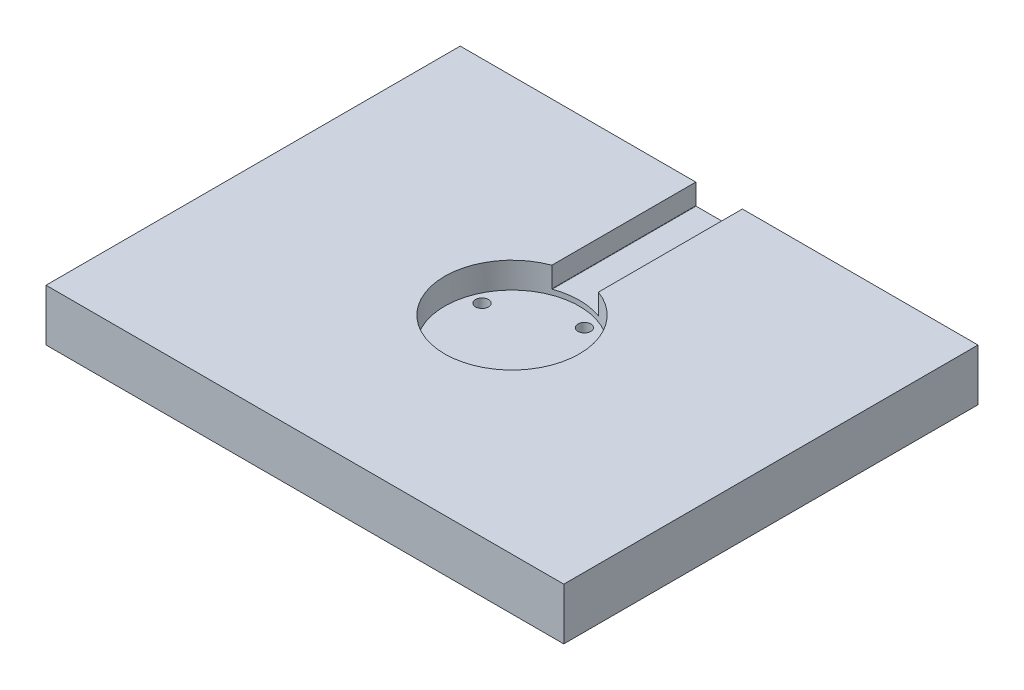
SolidWorks part; units mm, degrees
material "6061-T4 (SS)"
ref_plane "Front Plane" through (0, 0, 0) normal (0, 0, 1) x (1, 0, 0)
ref_plane "Top Plane" through (0, 0, 0) normal (0, 1, 0) x (1, 0, 0)
ref_plane "Right Plane" through (0, 0, 0) normal (1, 0, 0) x (0, 0, -1)
sketch "Sketch1" plane through (0, 0, 0) normal (0, 1, 0) x (1, 0, 0)
  line L1 (100, 80) -> (-100, 80)
  line L2 (100, 80) -> (100, -80)
  line L3 (100, -80) -> (-100, -80)
  line L4 (-100, 80) -> (-100, -80)
  line L5 (100, 80) -> (-100, -80) construction
  line L6 (100, -80) -> (-100, 80) construction
  point P0 (0, 0)
  dimension "D1" = 160
  dimension "D2" = 200
extrude "base" add sketch "Sketch1" along normal blind 20
sketch "Sketch2" plane through (0, 20, 0) normal (0, 1, 0) x (1, 0, 0)
  circle A0 centre (0, 0) radius 26
  dimension "D1" = 52
extrude "load cell cut" cut sketch "Sketch2" against normal blind 10 contours A0
sketch "post positioning points" plane through (0, 20, 0) normal (0, 1, 0) x (1, 0, 0)
  line L0 (-100, 80) -> (-100, -80) construction
  line L1 (-100, -80) -> (100, -80) construction
  line L2 (100, -80) -> (100, 80) construction
  line L3 (100, 80) -> (-100, 80) construction
  point P0 (-85, -65)
  point P5 (-25, 65)
  point P6 (-85, 65)
  point P7 (85, 65)
  point P8 (85, -65)
  point P9 (0, -65)
  point P10 (25, 65)
  dimension "D1" = 15
  dimension "D2" = 15
  dimension "D3" = 15
  dimension "D4" = 15
  dimension "D5" = 85
  dimension "D7" = 60
  dimension "D6" = 60
sketch "Sketch6" plane through (0, 0, -80) normal (0, 0, 1) x (1, 0, 0)
  line L0 (-100, 0) -> (100, 0) construction
  line L1 (9, 20) -> (-9, 20)
  line L2 (9, 20) -> (9, 12)
  line L3 (9, 12) -> (-9, 12)
  line L4 (-9, 20) -> (-9, 12)
  line L5 (9, 20) -> (-9, 12) construction
  line L6 (9, 12) -> (-9, 20) construction
  line L7 (-100, 20) -> (100, 20) construction
  point P0 (0, 16)
  point P8 (0, 0)
  dimension "D1" = 18
  dimension "D2" = 8
extrude "cut wire" cut sketch "Sketch6" along normal up to next contours L4 L3 L2 L1
sketch "Sketch7" plane through (0, 0, -80) normal (0, 0, 1) x (1, 0, 0)
  line L1 (5, 20) -> (-5, 20)
  line L2 (5, 20) -> (5, 10)
  line L3 (5, 10) -> (-5, 10)
  line L4 (-5, 20) -> (-5, 10)
  line L5 (5, 20) -> (-5, 10) construction
  line L6 (5, 10) -> (-5, 20) construction
  line L7 (-100, 0) -> (100, 0) construction
  line L8 (-100, 20) -> (100, 20) construction
  point P0 (0, 15)
  point P8 (0, 0)
  dimension "D1" = 10
  dimension "D2" = 10
extrude "cut wire 2" [suppressed] cut sketch "Sketch7" along normal up to next
fillet "Fillet5" [suppressed] radius 10
fillet "Fillet6" radius 0.1 2 edges at (9, 12, -52.1963) (-9, 12, -52.1963)
fillet "Fillet7" [suppressed] radius 5
sketch "Sketch12" plane through (0, 0, 0) normal (0, -1, 0) x (1, 0, 0)
  line L0 (0, 0) -> (100, 0) construction
  line L1 (19.771, 8.1894) -> (-8.1894, 19.771) construction
  line L2 (-8.1894, 19.771) -> (-19.771, -8.1894) construction
  line L3 (-19.771, -8.1894) -> (8.1894, -19.771) construction
  line L4 (8.1894, -19.771) -> (19.771, 8.1894) construction
  line L5 (100, 80) -> (100, -80) construction
  circle A0 centre (0, 0) radius 15.1321 construction
  dimension "D1" = 22.5
  dimension "D2" = 21.4
hole_wizard "Ø5.0mm Dowel Hole1" positions "3DSketch4" profile "Sketch13" hole size "Ø5.0" standard "ANSI Metric" end condition up to next
sketch3d "3DSketch4"
  point P0 (-8.1894, 0, 19.771)
  point P3 (19.771, 0, 8.1894)
  point P6 (8.1894, 0, -19.771)
  point P9 (-19.771, 0, -8.1894)
sketch "Sketch13" plane through (-8.1894, 0, 19.771) normal (1, 0, 0) x (0, 0, -1)
  line L0 (0, 0) -> (0, 10)
  line L1 (0, 10) -> (2.5, 10)
  line L2 (2.5, 10) -> (2.5, 0)
  line L5 (2.5, 0) -> (0, 0)
  line L11 (0, -6.35) -> (0, 107.95) construction
  dimension "Thru Hole Dia." = 5
  dimension "Thru Hole Depth" = 10
fillet "Fillet8" [suppressed] radius 5
equation "\"D2@post positioning points\" = \"D1@post positioning points\""
equation "\"D3@post positioning points\" = \"D1@post positioning points\""
equation "\"D4@post positioning points\" = \"D1@post positioning points\""
equation "\"D1@base\"   = 20"
equation "\"D1@load cell cut\"   = 10"
equation "\"D2@Sketch6\"=8"
